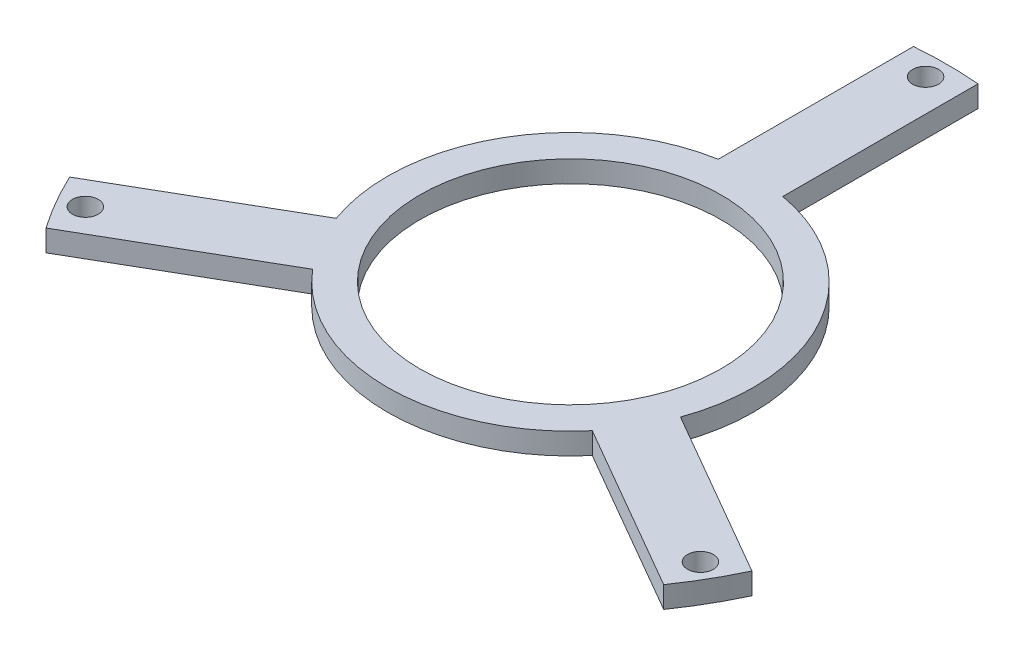
SolidWorks part; units mm, degrees
material "普通碳钢"
ref_plane "前视基准面" through (0, 0, 0) normal (0, 0, 1) x (1, 0, 0)
ref_plane "上视基准面" through (0, 0, 0) normal (0, 1, 0) x (1, 0, 0)
ref_plane "右视基准面" through (0, 0, 0) normal (1, 0, 0) x (0, 0, -1)
sketch "草图1" plane through (0, 0, 0) normal (0, 1, 0) x (1, 0, 0)
  line L0 (-178.4485, 0) -> (205.5695, 0) construction
  line L1 (0, 162.6695) -> (0, -174.216) construction
  line L2 (0, 0) -> (-214.8896, -124.0666) construction
  line L3 (0, 0) -> (208.6377, -120.457) construction
  line L4 (143.4967, -100.1684) -> (64.9569, -54.8234)
  line L5 (158.4967, -74.1876) -> (79.9569, -28.8426)
  line L6 (-15, 174.356) -> (-15, 83.666)
  line L7 (-158.4967, -74.1876) -> (-79.9569, -28.8426)
  line L8 (15, 174.356) -> (15, 83.666)
  line L9 (-143.4967, -100.1684) -> (-64.9569, -54.8234)
  arc A0 (-15, 83.666) -> (-79.9569, -28.8426) centre (0, 0) ccw
  arc A2 (-149.8025, -69.168) -> (-134.8025, -95.1488) centre (0, 0) ccw construction
  arc A3 (-158.4967, -74.1876) -> (-143.4967, -100.1684) centre (0, 0) ccw
  circle A4 centre (0, 0) radius 70
  arc A6 (-64.9569, -54.8234) -> (64.9569, -54.8234) centre (0, 0) ccw
  arc A7 (79.9569, -28.8426) -> (15, 83.666) centre (0, 0) ccw
  circle A9 centre (0, 165) radius 6
  circle A10 centre (142.8942, -82.5) radius 6
  circle A11 centre (-142.8942, -82.5) radius 6
  arc A12 (15, 174.356) -> (-15, 174.356) centre (0, 0) ccw
  arc A13 (15, 164.3168) -> (-15, 164.3168) centre (0, 0) ccw construction
  arc A14 (134.8025, -95.1488) -> (149.8025, -69.168) centre (0, 0) ccw construction
  arc A15 (143.4967, -100.1684) -> (158.4967, -74.1876) centre (0, 0) ccw
  point P11 (0, 109.6916)
  point P27 (0, 0)
  point P34 (0, 0)
  dimension "D1" = 350
  dimension "D2" = 330
  dimension "D4" = 170
  dimension "D5" = 140
  dimension "D10" = 12
  dimension "D6" = 120
  dimension "D7" = 120
  dimension "D8" = 30
  dimension "D9" = 3
  dimension "D11" = 3
extrude "凸台-拉伸1" add sketch "草图1" along normal blind 10
